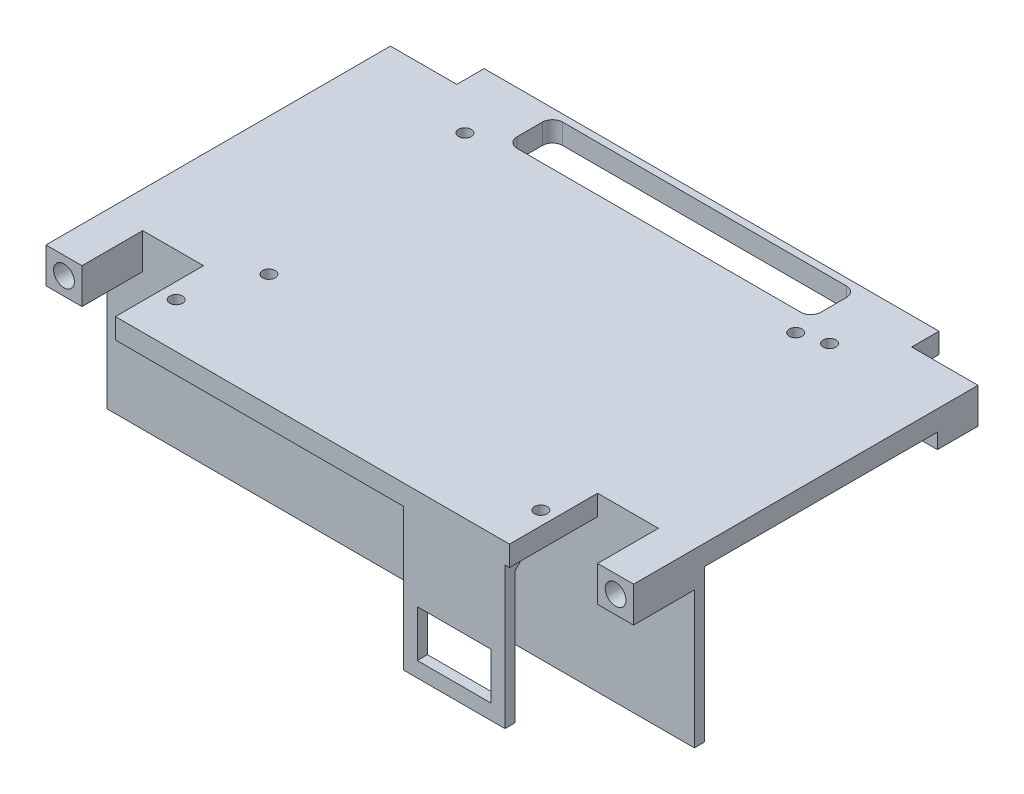
SolidWorks part; units mm, degrees
ref_plane "Front Plane" through (0, 0, 0) normal (0, 0, 1) x (1, 0, 0)
ref_plane "Top Plane" through (0, 0, 0) normal (0, 1, 0) x (1, 0, 0)
ref_plane "Right Plane" through (0, 0, 0) normal (1, 0, 0) x (0, 0, -1)
sketch "Sketch1" plane through (0, 0, 0) normal (0, 1, 0) x (1, 0, 0)
  line L0 (-58, 0) -> (58, 0) construction
  line L1 (-58, -34) -> (-50.9, -34)
  line L2 (-58, -34) -> (-58, 34)
  line L3 (-58, 34) -> (-50.9, 34)
  line L4 (58, -34) -> (58, 34)
  line L5 (-58, -34) -> (58, 34) construction
  line L6 (-58, 34) -> (58, -34) construction
  line L8 (-50.9, 34) -> (-50.9, 41)
  line L9 (-50.9, 41) -> (50.9, 41)
  line L10 (50.9, 34) -> (50.9, 41)
  line L11 (50.9, 34) -> (58, 34)
  line L12 (50.9, -34) -> (50.9, -41)
  line L13 (-50.9, -41) -> (50.9, -41)
  line L14 (-50.9, -34) -> (-50.9, -41)
  line L15 (50.9, -34) -> (58, -34)
  point P0 (0, 0)
  point P10 (0, 41)
  dimension "D1" = 116
  dimension "D2" = 68
  dimension "D3" = 7.1
  dimension "D4" = 7
extrude "Boss-Extrude1" add sketch "Sketch1" along normal blind 4
sketch "Sketch3" plane through (0, 0, 0) normal (0, -1, 0) x (1, 0, 0)
  line L0 (-58, -34) -> (-58, 34) construction
  line L1 (-50.9, -34) -> (-58, -34)
  line L2 (-50.9, -34) -> (-50.9, -26)
  line L3 (-50.9, -26) -> (-58, -26)
  line L4 (-58, -34) -> (-58, -26)
  dimension "D1" = 8
extrude "Boss-Extrude3" add sketch "Sketch3" along normal blind 3
sketch "Sketch4" plane through (0, 0, -34) normal (0, 0, -1) x (-1, 0, 0)
  line L0 (58, -3) -> (50.9, 4) construction
  circle A0 centre (54.45, 0.5) radius 2.05
  dimension "D1" = 4.1
extrude "Cut-Extrude1" cut sketch "Sketch4" against normal blind 7
mirror "Mirror1" about plane through (0, 0, 0) normal (1, 0, 0) of "Cut-Extrude1", "Boss-Extrude3"
mirror "Mirror2" about plane through (0, 0, 0) normal (0, 0, 1) of "Cut-Extrude1", "Boss-Extrude3", "Mirror1"
sketch "Sketch5" plane through (0, 4, 0) normal (0, 1, 0) x (1, 0, 0)
  line L0 (50.9, 41) -> (-50.9, 41) construction
  line L1 (-30, 38) -> (30, 38)
  line L2 (-30, 38) -> (-30, 29)
  line L3 (-30, 29) -> (30, 29)
  line L4 (30, 38) -> (30, 29)
  point P4 (0, 29)
  dimension "D1" = 3
  dimension "D2" = 9
  dimension "D3" = 60
extrude "Cut-Extrude2" cut sketch "Sketch5" against normal through all
sketch "Sketch6" plane through (0, 4, 0) normal (0, 1, 0) x (1, 0, 0)
  line L1 (-38.5, -28) -> (38.5, -28) construction
  line L2 (-38.5, -28) -> (-38.5, 24) construction
  line L3 (-38.5, 24) -> (38.5, 24) construction
  line L4 (38.5, -28) -> (38.5, 24) construction
  line L5 (-38.5, -28) -> (38.5, 24) construction
  line L6 (-38.5, 24) -> (38.5, -28) construction
  circle A0 centre (-38.5, 24) radius 1.25
  circle A1 centre (38.5, 24) radius 1.25
  circle A2 centre (38.5, -28) radius 1.25
  circle A3 centre (-38.5, -28) radius 1.25
  point P0 (0, -2)
  point P9 (0, -2)
  dimension "D4" = 2.5
  dimension "D1" = 77
  dimension "D2" = 52
  dimension "D3" = 2
fillet "Fillet1" radius 2 4 edges at (-30, 2, -38) (-30, 2, -29) (30, 2, -38) (30, 2, -29)
sketch "Sketch7" plane through (0, 4, 0) normal (0, 1, 0) x (1, 0, 0)
  line L0 (50.9, 34) -> (50.9, 41) construction
  line L1 (-50.9, 41) -> (50.9, 41)
  line L2 (-50.9, 41) -> (-50.9, 40)
  line L3 (-50.9, 40) -> (50.9, 40)
  line L4 (50.9, 41) -> (50.9, 40)
  line L5 (-50.9, -34) -> (-50.9, -41) construction
  line L6 (50.9, -41) -> (-50.9, -41)
  line L7 (50.9, -41) -> (50.9, -40)
  line L8 (50.9, -40) -> (-50.9, -40)
  line L9 (-50.9, -41) -> (-50.9, -40)
  dimension "D1" = 1
  dimension "D2" = 1
extrude "Cut-Extrude3" cut sketch "Sketch7" against normal through all
sketch "Sketch8" plane through (0, 0, 0) normal (0, -1, 0) x (1, 0, 0)
  line L0 (58, 26) -> (58, -26) construction
  line L1 (58, 22) -> (-58, 22)
  line L2 (58, 22) -> (58, 20)
  line L3 (58, 20) -> (-58, 20)
  line L4 (-58, 22) -> (-58, 20)
  line L5 (-58, -26) -> (-58, 26) construction
  line L7 (50.9, 40) -> (-50.9, 40) construction
  dimension "D1" = 20
  dimension "D2" = 2
extrude "Boss-Extrude4" add sketch "Sketch8" along normal blind 30
sketch "Sketch9" plane through (0, 4, 0) normal (0, 1, 0) x (1, 0, 0)
  line L0 (58, -22) -> (-58, -22) construction
  line L1 (-50.9, -40) -> (-38.9, -40)
  line L2 (-50.9, -40) -> (-50.9, -22)
  line L3 (-50.9, -22) -> (-38.9, -22)
  line L4 (-38.9, -40) -> (-38.9, -22)
  dimension "D1" = 12
extrude "Cut-Extrude4" cut sketch "Sketch9" against normal blind 10
sketch "Sketch10" plane through (0, -3, 0) normal (0, -1, 0) x (1, 0, 0)
  line L1 (-58, 26) -> (-50.9, 26)
  line L2 (-58, 26) -> (-58, 22)
  line L3 (-58, 22) -> (-50.9, 22)
  line L4 (-50.9, 26) -> (-50.9, 22)
  line L5 (50.9, 26) -> (58, 26)
  line L6 (50.9, 26) -> (50.9, 22)
  line L7 (50.9, 22) -> (58, 22)
  line L8 (58, 26) -> (58, 22)
extrude "Boss-Extrude5" add sketch "Sketch10" against normal up to surface (3 mm away) up to face at (27.2714, 0, 30)
ref_plane "Plane2" through (-51, 0, 0) normal (-1, 0, 0) x (0, 0, 1)
sketch "Sketch12" plane through (-51, 0, 0) normal (-1, 0, 0) x (0, 0, 1)
  line L0 (22, -5.8) -> (22, -16.2)
  line L1 (22, -30) -> (22, -3) construction
  line L2 (22, -16.2) -> (24.7, -13.5)
  line L3 (24.7, -13.5) -> (24.7, -8.5)
  line L4 (24.7, -8.5) -> (22, -5.8)
  line L5 (24.7, -11) -> (22, -11) construction
  line L6 (22, -3) -> (34, -3) construction
  line L7 (24.1, -9) -> (22.6, -9)
  line L8 (24.1, -9) -> (24.1, -13)
  line L9 (24.1, -13) -> (22.6, -13)
  line L10 (22.6, -9) -> (22.6, -13)
  line L11 (22, -20.8) -> (22, -31.2)
  line L12 (22, -31.2) -> (24.7, -28.5)
  line L13 (24.7, -28.5) -> (24.7, -23.5)
  line L14 (24.7, -23.5) -> (22, -20.8)
  line L15 (24.1, -24) -> (22.6, -24)
  line L16 (24.1, -24) -> (24.1, -28)
  line L17 (24.1, -28) -> (22.6, -28)
  line L18 (22.6, -24) -> (22.6, -28)
  line L19 (24.7, -26) -> (22, -26) construction
  point P13 (23.35, -11)
  point P14 (24.1, -11)
  dimension "D1" = 1.5
  dimension "D2" = 0.6
  dimension "D3" = 0.6
  dimension "D4" = 4
  dimension "D5" = 45
  dimension "D6" = 5
  dimension "D7" = 8
  dimension "D8" = 2
extrude "Boss-Extrude6" add sketch "Sketch12" against normal blind 2
ref_plane "Plane3" through (-44.9, 0, 0) normal (1, 0, 0) x (0, 0, -1)
mirror "Mirror3" about plane through (-44.9, 0, 0) normal (1, 0, 0) of "Boss-Extrude6"
sketch "Sketch13" plane through (0, 0, 0) normal (0, -1, 0) x (1, 0, 0)
  line L0 (-28, -29) -> (28, -29) construction
  line L1 (-18, -19.5) -> (18, -19.5)
  line L2 (-18, -19.5) -> (-18, -21.5)
  line L3 (-18, -21.5) -> (18, -21.5)
  line L4 (18, -19.5) -> (18, -21.5)
  point P4 (0, -21.5)
  dimension "D1" = 36
  dimension "D2" = 2
  dimension "D3" = 7.5
extrude "Boss-Extrude7" add sketch "Sketch13" along normal up to surface (30 mm away) up to face at (-22.45, -30, 21.5)
sketch "Sketch14" plane through (0, 0, 0) normal (1, 0, 0) x (0, 0, -1)
  line L3 (-0.25, -38) -> (-0.25, 0) construction
  line L4 (-20, 0) -> (26, 0) construction
  line L13 (-24.1, -13) -> (-24.1, -9) construction
  line L14 (-24.1, -9) -> (-22.6, -9) construction
  line L15 (-22.6, -9) -> (-22.6, -13) construction
  line L16 (-22.6, -13) -> (-24.1, -13) construction
  line L17 (-22, -5.8) -> (-22, -16.2) construction
  line L18 (-22, -16.2) -> (-24.7, -13.5) construction
  line L19 (-24.7, -13.5) -> (-24.7, -8.5) construction
  line L20 (-24.7, -8.5) -> (-22, -5.8) construction
  line L29 (-24.1, -13) -> (-24.1, -9) construction
  line L30 (-24.1, -9) -> (-22.6, -9) construction
  line L31 (-22.6, -9) -> (-22.6, -13) construction
  line L32 (-22.6, -13) -> (-24.1, -13) construction
  line L33 (-22, -5.8) -> (-22, -16.2) construction
  line L34 (-22, -16.2) -> (-24.7, -13.5) construction
  line L35 (-24.7, -13.5) -> (-24.7, -8.5) construction
  line L36 (-24.7, -8.5) -> (-22, -5.8) construction
  line L37 (24.2, -8.5) -> (21.5, -5.8)
  line L38 (24.2, -13.5) -> (24.2, -8.5)
  line L39 (21.5, -16.2) -> (24.2, -13.5)
  line L40 (21.5, -5.8) -> (21.5, -16.2)
  line L41 (22.1, -13) -> (23.6, -13)
  line L42 (22.1, -9) -> (22.1, -13)
  line L43 (23.6, -9) -> (22.1, -9)
  line L44 (23.6, -13) -> (23.6, -9)
extrude "Boss-Extrude8" add sketch "Sketch14" along normal mid plane 2
sketch "Sketch15" plane through (0, 0, 0) normal (1, 0, 0) x (0, 0, -1)
  line L0 (19.5, 0) -> (19.5, -5)
  line L1 (19.5, -30) -> (19.5, 0) construction
  line L2 (19.5, -5) -> (16.6132, 0)
  line L3 (-20, 0) -> (26, 0) construction
  line L4 (16.6132, 0) -> (19.5, 0)
  dimension "D1" = 60
  dimension "D2" = 5
extrude "Boss-Extrude9" add sketch "Sketch15" against normal up to surface and the other way up to surface up to face at (-18, -15, -20.5) other way up to face at (18, -15, -20.5)
sketch "Sketch16" plane through (0, 0, 40) normal (0, 0, 1) x (1, 0, 0)
  line L0 (38, 0) -> (18, -28) construction
  line L1 (38, 0) -> (18, 0)
  line L2 (38, 0) -> (38, -28)
  line L3 (38, -28) -> (18, -28)
  line L4 (18, 0) -> (18, -28)
  line L5 (50.9, 0) -> (-38.9, 0) construction
  line L6 (20.7, -15.8) -> (35.3, -15.8)
  line L7 (20.7, -15.8) -> (20.7, -25)
  line L8 (20.7, -25) -> (35.3, -25)
  line L9 (35.3, -15.8) -> (35.3, -25)
  line L10 (20.7, -15.8) -> (35.3, -25) construction
  line L11 (20.7, -25) -> (35.3, -15.8) construction
  line L12 (58, -30) -> (58, -3) construction
  point P5 (28, -14)
  point P10 (28, -20.4)
  dimension "D1" = 20
  dimension "D2" = 28
  dimension "D3" = 14.6
  dimension "D4" = 9.2
  dimension "D5" = 20
  dimension "D6" = 3
extrude "Boss-Extrude10" add sketch "Sketch16" against normal blind 2.6
sketch "Sketch17" plane through (0, 0, 0) normal (0, -1, 0) x (1, 0, 0)
  line L6 (-38.9, 22) -> (-50.9, 22) construction
  line L7 (50.9, 40) -> (38.9, 40)
  line L8 (50.9, 40) -> (50.9, 22)
  line L9 (50.9, 22) -> (38.9, 22)
  line L10 (38.9, 40) -> (38.9, 22)
  line L13 (-38.9, 40) -> (-38.9, 22) construction
extrude "Cut-Extrude5" cut sketch "Sketch17" against normal through all
sketch "Sketch18" plane through (0, 4, 0) normal (0, 1, 0) x (1, 0, 0)
  line L5 (-50.9, 40) -> (50.9, 40) construction
  line L6 (50.9, 34) -> (44.9, 34)
  line L7 (50.9, 34) -> (50.9, 40)
  line L8 (50.9, 40) -> (44.9, 40)
  line L9 (44.9, 34) -> (44.9, 40)
  line L11 (-50.9, 34) -> (-44.9, 34)
  line L12 (-50.9, 34) -> (-50.9, 40)
  line L13 (-50.9, 40) -> (-44.9, 40)
  line L14 (-44.9, 34) -> (-44.9, 40)
extrude "Cut-Extrude6" cut sketch "Sketch18" against normal through all
sketch "Sketch20" plane through (0, 4, 0) normal (0, 1, 0) x (1, 0, 0)
  line L0 (-31, 25) -> (31, -17) construction
  line L1 (-31, 25) -> (31, 25) construction
  line L2 (-31, 25) -> (-31, -17) construction
  line L3 (-31, -17) -> (31, -17) construction
  line L4 (31, 25) -> (31, -17) construction
  line L5 (-38.5, 26) -> (38.5, 26) construction
  line L6 (-38.5, 26) -> (-38.5, -26) construction
  line L7 (-38.5, -26) -> (38.5, -26) construction
  line L8 (38.5, 26) -> (38.5, -26) construction
  line L11 (38.5, 26) -> (-38.5, -26) construction
  circle A0 centre (-31, 25) radius 3 construction
  circle A1 centre (-31, -17) radius 3 construction
  circle A2 centre (31, -17) radius 3 construction
  circle A3 centre (31, 25) radius 3 construction
  circle A4 centre (-38.5, 26) radius 3 construction
  circle A5 centre (38.5, 26) radius 3 construction
  circle A6 centre (38.5, -26) radius 3 construction
  circle A7 centre (-38.5, -26) radius 3 construction
  point P18 (0, 4)
  dimension "D3" = 6
  dimension "D1" = 42
  dimension "D2" = 62
  dimension "D4" = 4
  dimension "D6" = 77
  dimension "D7" = 52
sketch "Sketch22" plane through (0, 4, 0) normal (0, 1, 0) x (1, 0, 0)
  circle A0 centre (-31, 25) radius 1.25 construction
  circle A1 centre (31, 25) radius 1.25
  circle A2 centre (31, -17) radius 1.25 construction
  circle A3 centre (-31, -17) radius 1.25
  dimension "D1" = 2.5
extrude "Cut-Extrude7" cut sketch "Sketch22" against normal up to surface (4 mm away) up to face at (14, 0, 34.85)
sketch "Sketch25" plane through (0, 0, -21.5) normal (0, 0, -1) x (-1, 0, 0)
  line L0 (58, -30) -> (-58, -30) construction
  line L1 (-18, -30) -> (-12, -30)
  line L2 (-18, -30) -> (-18, 0)
  line L3 (-18, 0) -> (-12, 0)
  line L4 (-12, -30) -> (-12, 0)
  line L5 (-18, -30) -> (-18, 0) construction
  line L6 (18, 0) -> (-18, 0) construction
  line L7 (-18, -30) -> (18, -30) construction
  line L8 (18, 0) -> (12, 0)
  line L9 (18, 0) -> (18, -30)
  line L10 (18, -30) -> (12, -30)
  line L11 (12, 0) -> (12, -30)
  dimension "D1" = 6
extrude "Cut-Extrude11" cut sketch "Sketch25" against normal blind 10
sketch "Sketch26" plane through (-1, 0, 0) normal (-1, 0, 0) x (0, 0, 1)
  line L1 (-21.5, -5.8) -> (-27.2016, -5.8)
  line L2 (-21.5, -5.8) -> (-21.5, -36.3625)
  line L3 (-21.5, -36.3625) -> (-27.2016, -36.3625)
  line L4 (-27.2016, -5.8) -> (-27.2016, -36.3625)
  line L5 (22, -5.8) -> (28.5342, -5.8)
  line L6 (22, -5.8) -> (22, -34.3243)
  line L7 (22, -34.3243) -> (28.5342, -34.3243)
  line L8 (28.5342, -5.8) -> (28.5342, -34.3243)
extrude "Cut-Extrude12" cut sketch "Sketch26" against normal through all both and the other way through all
sketch "Sketch27" plane through (0, 4, 0) normal (0, 1, 0) x (1, 0, 0)
  line L1 (-35.8, -30.5) -> (36.2, -30.5) construction
  line L2 (-35.8, -30.5) -> (-35.8, 26.5) construction
  line L3 (-35.8, 26.5) -> (36.2, 26.5) construction
  line L4 (36.2, -30.5) -> (36.2, 26.5) construction
  line L5 (-35.8, -30.5) -> (36.2, 26.5) construction
  line L6 (-35.8, 26.5) -> (36.2, -30.5) construction
  circle A0 centre (-35.8, 26.5) radius 1.25
  circle A1 centre (-35.8, -30.5) radius 1.25
  circle A2 centre (36.2, -30.5) radius 1.25
  circle A3 centre (36.2, 26.5) radius 1.25
  circle A5 centre (31, 25) radius 1.25 construction
  circle A6 centre (31, 25) radius 1.25 construction
  point P0 (0.2, -2)
  dimension "D1" = 72
  dimension "D2" = 57
  dimension "D3" = 2
  dimension "D4" = 0.2
extrude "Cut-Extrude13" cut sketch "Sketch27" against normal through all
sketch "Sketch28" plane through (0, 4, 0) normal (0, 1, 0) x (1, 0, 0)
  line L0 (44.9, 40) -> (44.9, 34) construction
  line L1 (-44.9, 40) -> (44.9, 40)
  line L2 (-44.9, 40) -> (-44.9, 39.4)
  line L3 (-44.9, 39.4) -> (44.9, 39.4)
  line L4 (44.9, 40) -> (44.9, 39.4)
  line L5 (-38.9, -40) -> (-38.9, -22) construction
  line L6 (38.9, -40) -> (-38.9, -40)
  line L7 (38.9, -40) -> (38.9, -39.4)
  line L8 (38.9, -39.4) -> (-38.9, -39.4)
  line L9 (-38.9, -40) -> (-38.9, -39.4)
  dimension "D1" = 0.6
  dimension "D2" = 0.6
extrude "Cut-Extrude14" cut sketch "Sketch28" against normal through all
chamfer "Chamfer1" distance 2 angle 45 1 edges at (28, 0, 37.4)
